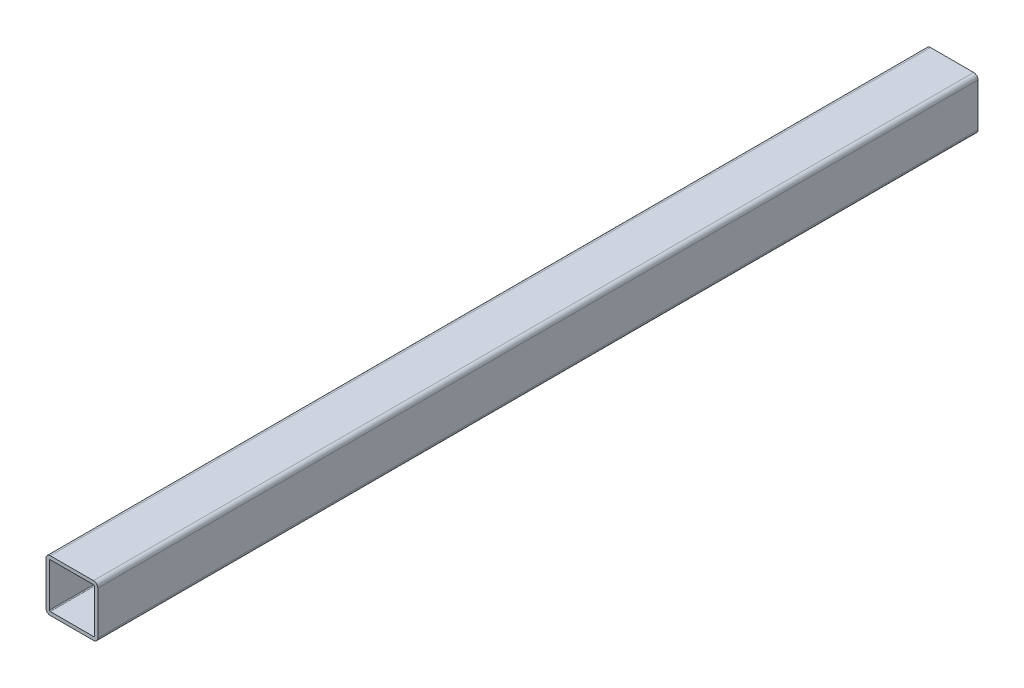
SolidWorks part; units mm, degrees
ref_plane "Front Plane" through (0, 0, 0) normal (0, 0, 1) x (1, 0, 0)
ref_plane "Top Plane" through (0, 0, 0) normal (0, 1, 0) x (1, 0, 0)
ref_plane "Right Plane" through (0, 0, 0) normal (1, 0, 0) x (0, 0, -1)
sketch "Sketch1" plane through (0, 0, 0) normal (0, 0, 1) x (1, 0, 0)
  line L1 (-15.875, 19.05) -> (15.875, 19.05)
  line L2 (-19.05, 15.875) -> (-19.05, -15.875)
  line L3 (-15.875, -19.05) -> (15.875, -19.05)
  line L4 (19.05, 15.875) -> (19.05, -15.875)
  line L5 (-19.05, 19.05) -> (19.05, -19.05) construction
  line L6 (-19.05, -19.05) -> (19.05, 19.05) construction
  arc A0 (-19.05, -15.875) -> (-15.875, -19.05) centre (-15.875, -15.875) ccw
  arc A1 (15.875, -19.05) -> (19.05, -15.875) centre (15.875, -15.875) ccw
  arc A2 (19.05, 15.875) -> (15.875, 19.05) centre (15.875, 15.875) ccw
  arc A3 (-15.875, 19.05) -> (-19.05, 15.875) centre (-15.875, 15.875) ccw
  point P0 (0, 0)
  dimension "D3" = 3.175
  dimension "D1" = 38.1
  dimension "D2" = 38.1
extrude "Extrude-Thin1" add sketch "Sketch1" along normal mid plane 647.7 thin
sketch "Sketch2" plane through (0, 19.05, 0) normal (0, 1, 0) x (1, 0, 0)
  line L0 (0, 323.85) -> (0, -323.85) construction
  line L1 (15.875, 323.85) -> (-15.875, 323.85) construction
  line L2 (15.875, -323.85) -> (-15.875, -323.85) construction
  line L3 (-15.875, 304.8) -> (15.875, 304.8) construction
  line L4 (-15.875, -323.85) -> (-15.875, 323.85) construction
  line L5 (15.875, -323.85) -> (15.875, 323.85) construction
  line L6 (-15.875, -228.6) -> (15.875, -228.6) construction
  line L8 (-15.875, 228.6) -> (15.875, 228.6) construction
  line L9 (-15.875, 152.4) -> (15.875, 152.4) construction
  line L10 (-15.875, 76.2) -> (15.875, 76.2) construction
  line L11 (-15.875, -152.4) -> (15.875, -152.4) construction
  line L12 (-15.875, 0) -> (15.875, 0) construction
  line L13 (-15.875, -76.2) -> (15.875, -76.2) construction
  line L14 (-15.875, -304.8) -> (15.875, -304.8) construction
  dimension "D1" = 19.05
  dimension "D2" = 76.2
  dimension "D3" = 76.2
  dimension "D4" = 76.2
  dimension "D5" = 76.2
  dimension "D6" = 76.2
  dimension "D7" = 76.2
  dimension "D8" = 76.2
  dimension "D9" = 76.2
